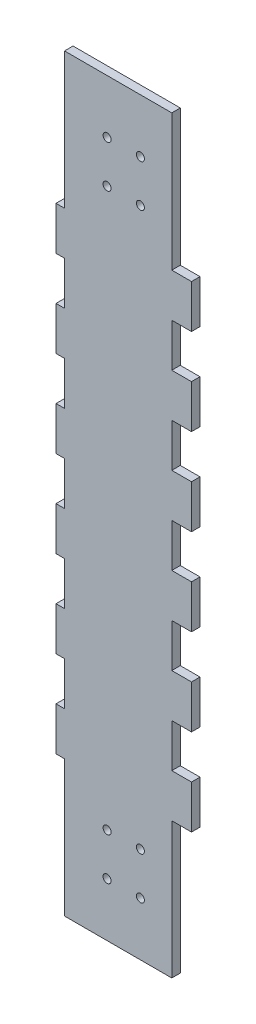
SolidWorks part; units mm, degrees
material "Acrylic (Medium-high impact)"
ref_plane "Front Plane" through (0, 0, 0) normal (0, 0, 1) x (1, 0, 0)
ref_plane "Top Plane" through (0, 0, 0) normal (0, 1, 0) x (1, 0, 0)
ref_plane "Right Plane" through (0, 0, 0) normal (1, 0, 0) x (0, 0, -1)
sketch "Sketch1" plane through (0, 0, 0) normal (0, 0, 1) x (1, 0, 0)
  line L5 (0, 279.4) -> (40, 279.4)
  line L87 (40, 0) -> (0, 0)
  line L88 (20, 279.4) -> (20, 0) construction
  line L89 (40, 139.7) -> (0, 139.7) construction
  line L90 (0, 0) -> (-3.175, 0)
  line L91 (-3.175, 0) -> (-3.175, 50.8)
  line L92 (-3.175, 50.8) -> (0, 50.8)
  line L93 (0, 50.8) -> (0, 0)
  line L94 (0, 228.6) -> (0, 279.4)
  line L95 (-3.175, 228.6) -> (0, 228.6)
  line L96 (-3.175, 279.4) -> (-3.175, 228.6)
  line L97 (0, 279.4) -> (-3.175, 279.4)
  line L98 (0, 50.8) -> (-3.175, 50.8)
  line L99 (-3.175, 50.8) -> (-3.175, 66.9636)
  line L100 (-3.175, 66.9636) -> (0, 66.9636)
  line L101 (0, 66.9636) -> (0, 50.8)
  line L110 (40, 0) -> (47.35, 0)
  line L111 (47.35, 0) -> (47.35, 50.8)
  line L112 (47.35, 50.8) -> (40, 50.8)
  line L113 (-3.175, 66.9636) -> (-3.175, 83.1273)
  line L114 (-3.175, 66.9636) -> (0, 66.9636)
  line L115 (0, 83.1273) -> (0, 66.9636)
  line L116 (-3.175, 83.1273) -> (0, 83.1273)
  line L117 (-3.175, 83.1273) -> (-3.175, 99.2909)
  line L118 (-3.175, 83.1273) -> (0, 83.1273)
  line L119 (0, 99.2909) -> (0, 83.1273)
  line L120 (-3.175, 99.2909) -> (0, 99.2909)
  line L121 (-3.175, 99.2909) -> (-3.175, 115.4545)
  line L122 (-3.175, 99.2909) -> (0, 99.2909)
  line L123 (0, 115.4545) -> (0, 99.2909)
  line L124 (-3.175, 115.4545) -> (0, 115.4545)
  line L125 (-3.175, 115.4545) -> (-3.175, 131.6182)
  line L126 (-3.175, 115.4545) -> (0, 115.4545)
  line L127 (0, 131.6182) -> (0, 115.4545)
  line L128 (-3.175, 131.6182) -> (0, 131.6182)
  line L129 (-3.175, 131.6182) -> (-3.175, 147.7818)
  line L130 (-3.175, 131.6182) -> (0, 131.6182)
  line L131 (0, 147.7818) -> (0, 131.6182)
  line L132 (-3.175, 147.7818) -> (0, 147.7818)
  line L133 (-3.175, 147.7818) -> (-3.175, 163.9455)
  line L134 (-3.175, 147.7818) -> (0, 147.7818)
  line L135 (0, 163.9455) -> (0, 147.7818)
  line L136 (-3.175, 163.9455) -> (0, 163.9455)
  line L137 (-3.175, 163.9455) -> (-3.175, 180.1091)
  line L138 (-3.175, 163.9455) -> (0, 163.9455)
  line L139 (0, 180.1091) -> (0, 163.9455)
  line L140 (-3.175, 180.1091) -> (0, 180.1091)
  line L141 (-3.175, 180.1091) -> (-3.175, 196.2727)
  line L142 (-3.175, 180.1091) -> (0, 180.1091)
  line L143 (0, 196.2727) -> (0, 180.1091)
  line L144 (-3.175, 196.2727) -> (0, 196.2727)
  line L145 (-3.175, 196.2727) -> (-3.175, 212.4364)
  line L146 (-3.175, 196.2727) -> (0, 196.2727)
  line L147 (0, 212.4364) -> (0, 196.2727)
  line L148 (-3.175, 212.4364) -> (0, 212.4364)
  line L149 (-3.175, 50.8) -> (-3.175, 66.9636) construction
  line L150 (0, 279.4) -> (0, 0)
  line L187 (40, 50.8) -> (40, 0)
  line L188 (47.35, 83.1273) -> (40, 83.1273)
  line L189 (-3.175, 212.4364) -> (-3.175, 228.6)
  line L190 (-3.175, 212.4364) -> (0, 212.4364)
  line L191 (0, 228.6) -> (0, 212.4364)
  line L192 (-3.175, 228.6) -> (0, 228.6)
  line L194 (40, 279.4) -> (47.35, 279.4)
  line L195 (47.35, 279.4) -> (47.35, 228.6)
  line L196 (47.35, 228.6) -> (40, 228.6)
  line L197 (40, 228.6) -> (40, 279.4)
  line L198 (40, 50.8) -> (47.35, 50.8)
  line L199 (47.35, 50.8) -> (47.35, 66.9636)
  line L200 (47.35, 66.9636) -> (40, 66.9636)
  line L201 (40, 66.9636) -> (40, 50.8)
  line L202 (40, 83.1273) -> (40, 66.9636)
  line L203 (47.35, 66.9636) -> (47.35, 83.1273)
  line L204 (47.35, 66.9636) -> (40, 66.9636)
  line L205 (47.35, 99.2909) -> (40, 99.2909)
  line L206 (40, 99.2909) -> (40, 83.1273)
  line L207 (47.35, 83.1273) -> (47.35, 99.2909)
  line L208 (47.35, 83.1273) -> (40, 83.1273)
  line L209 (47.35, 115.4545) -> (40, 115.4545)
  line L210 (40, 115.4545) -> (40, 99.2909)
  line L211 (47.35, 99.2909) -> (47.35, 115.4545)
  line L212 (47.35, 99.2909) -> (40, 99.2909)
  line L213 (47.35, 131.6182) -> (40, 131.6182)
  line L214 (40, 131.6182) -> (40, 115.4545)
  line L215 (47.35, 115.4545) -> (47.35, 131.6182)
  line L216 (47.35, 115.4545) -> (40, 115.4545)
  line L217 (47.35, 147.7818) -> (40, 147.7818)
  line L218 (40, 147.7818) -> (40, 131.6182)
  line L219 (47.35, 131.6182) -> (47.35, 147.7818)
  line L220 (47.35, 131.6182) -> (40, 131.6182)
  line L221 (47.35, 163.9455) -> (40, 163.9455)
  line L222 (40, 163.9455) -> (40, 147.7818)
  line L223 (47.35, 147.7818) -> (47.35, 163.9455)
  line L224 (47.35, 147.7818) -> (40, 147.7818)
  line L225 (47.35, 180.1091) -> (40, 180.1091)
  line L226 (40, 180.1091) -> (40, 163.9455)
  line L227 (47.35, 163.9455) -> (47.35, 180.1091)
  line L228 (47.35, 163.9455) -> (40, 163.9455)
  line L229 (47.35, 196.2727) -> (40, 196.2727)
  line L230 (40, 196.2727) -> (40, 180.1091)
  line L231 (47.35, 180.1091) -> (47.35, 196.2727)
  line L232 (47.35, 180.1091) -> (40, 180.1091)
  line L233 (47.35, 212.4364) -> (40, 212.4364)
  line L234 (40, 212.4364) -> (40, 196.2727)
  line L235 (47.35, 196.2727) -> (47.35, 212.4364)
  line L236 (47.35, 196.2727) -> (40, 196.2727)
  line L237 (47.35, 228.6) -> (40, 228.6)
  line L238 (40, 228.6) -> (40, 212.4364)
  line L239 (47.35, 212.4364) -> (47.35, 228.6)
  line L240 (47.35, 212.4364) -> (40, 212.4364)
  line L241 (47.35, 66.9636) -> (47.35, 83.1273) construction
  line L242 (40, 279.4) -> (40, 0)
  dimension "D1" = 279.4
  dimension "D3" = 50.8
  dimension "D4" = 3.175
  dimension "D5" = 16.1636
  dimension "D7" = 16.1636
  dimension "D2" = 40
  dimension "D8" = 50.8
  dimension "D9" = 50.8
  dimension "D10" = 16.1636
  dimension "D12" = 16.1636
  dimension "D13" = 7.35
  dimension "D6" = 11
  dimension "D11" = 11
extrude "Boss-Extrude1" add sketch "Sketch1" along normal blind 3.175
sketch "Sketch2" plane through (0, 0, 3.175) normal (0, 0, 1) x (1, 0, 0)
  line L0 (20, 0) -> (20, 279.4) construction
  line L1 (47.35, 50.8) -> (47.35, 66.9636) construction
  line L2 (40, 0) -> (0, 0) construction
  line L3 (20, 139.7) -> (0, 139.7) construction
  line L4 (0, 131.6182) -> (0, 147.7818) construction
  line L5 (-3.175, 50.8) -> (-3.175, 66.9636) construction
  line L6 (40, 0) -> (0, 0) construction
  circle A0 centre (15.875, 20) radius 1.5
  circle A1 centre (15.875, 35.75) radius 1.5
  circle A2 centre (15.875, 243.65) radius 1.5
  circle A3 centre (15.875, 259.4) radius 1.5
  circle A5 centre (28.3, 20) radius 1.5
  circle A6 centre (28.3, 35.75) radius 1.5
  circle A7 centre (28.3, 243.65) radius 1.5
  circle A8 centre (28.3, 259.4) radius 1.5
  point P3 (20, 0)
  point P22 (0, 0)
  dimension "D1" = 3
  dimension "D2" = 3
  dimension "D6" = 3
  dimension "D7" = 3
  dimension "D3" = 15.75
  dimension "D4" = 19.05
  dimension "D5" = 20
  dimension "D8" = 19.05
  dimension "D9" = 15.75
  dimension "D10" = 20
extrude "Cut-Extrude1" cut sketch "Sketch2" against normal up to surface (3.175 mm away) up to face at (20.9635, 139.7, 0)
equation "\"D7@Sketch1\"=\"D5@Sketch1\""
equation "\"D5@Sketch1\"=((\"D1@Sketch1\"-2*\"D3@Sketch1\")/(\"D6@Sketch1\"))"
equation "\"D8@Sketch1\"=\"D3@Sketch1\""
equation "\"D9@Sketch1\"=\"D3@Sketch1\""
equation "\"D10@Sketch1\"=((\"D1@Sketch1\"-2*\"D8@Sketch1\")/(\"D6@Sketch1\"))"
equation "\"D12@Sketch1\"=\"D10@Sketch1\""
equation "\"D13@Sketch1\"=2*\"D4@Sketch1\"+1mm"
equation "\"D8@Sketch2\"=\"D4@Sketch2\""
equation "\"D9@Sketch2\"=\"D3@Sketch2\""
equation "\"D10@Sketch2\"=\"D5@Sketch2\""
